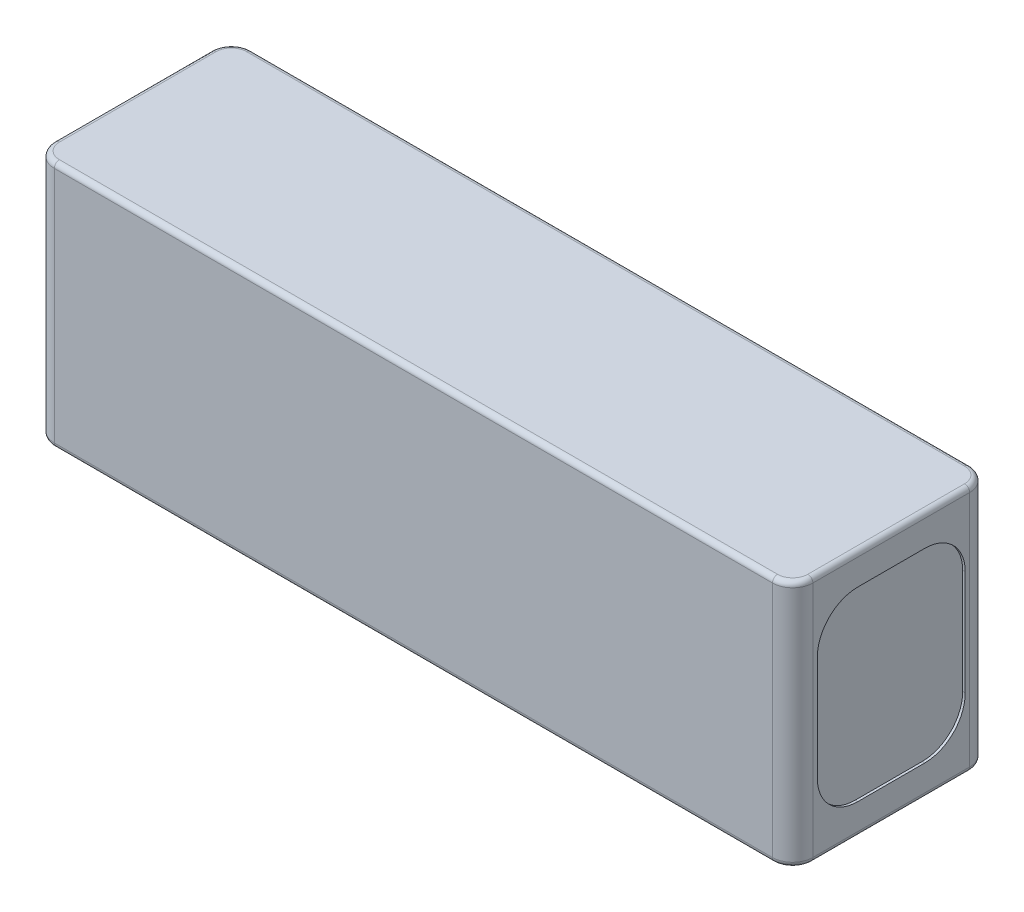
SolidWorks part; units mm, degrees
ref_plane "Front Plane" through (0, 0, 0) normal (0, 0, 1) x (1, 0, 0)
ref_plane "Top Plane" through (0, 0, 0) normal (0, 1, 0) x (1, 0, 0)
ref_plane "Right Plane" through (0, 0, 0) normal (1, 0, 0) x (0, 0, -1)
ref_plane "Plane1" through (0, 0, -15) normal (0, 0, -1) x (-1, 0, 0)
sketch "Sketch1" plane through (0, 0, -15) normal (0, 0, -1) x (-1, 0, 0)
  line L0 (-69, -22) -> (81, -22)
  line L1 (81, -22) -> (81, 27)
  line L2 (81, 27) -> (-69, 27)
  line L3 (-69, 27) -> (-69, -22)
  line L4 (-69, 2.5) -> (81, 2.5) construction
  line L5 (6, 27) -> (6, -22) construction
  dimension "D1" = 49
  dimension "D2" = 150
extrude "Boss-Extrude1" add sketch "Sketch1" against normal blind 39
sketch "Sketch2" plane through (69, 0, 0) normal (1, 0, 0) x (0, 0, -1)
  line L0 (-19.125, 12.875) -> (-19.125, -7.875)
  line L1 (-11.125, -15.875) -> (2.125, -15.875)
  line L2 (10.125, -7.875) -> (10.125, 12.875)
  line L3 (2.125, 20.875) -> (-11.125, 20.875)
  line L4 (-24, 27) -> (15, -22) construction
  line L5 (15, 27) -> (-24, -22) construction
  line L6 (-19.125, 20.875) -> (10.125, -15.875) construction
  line L7 (10.125, 20.875) -> (-19.125, -15.875) construction
  line L12 (-24, 27) -> (15, 27) construction
  line L13 (-24, 27) -> (-24, -22) construction
  line L14 (-24, -22) -> (15, -22) construction
  line L15 (15, 27) -> (15, -22) construction
  line L16 (-24, 27) -> (15, -22) construction
  line L17 (-24, -22) -> (15, 27) construction
  arc A0 (-19.125, -7.875) -> (-11.125, -15.875) centre (-11.125, -7.875) ccw
  arc A1 (2.125, -15.875) -> (10.125, -7.875) centre (2.125, -7.875) ccw
  arc A2 (10.125, 12.875) -> (2.125, 20.875) centre (2.125, 12.875) ccw
  arc A3 (-19.125, 12.875) -> (-11.125, 20.875) centre (-11.125, 12.875) cw
  point P16 (-4.5, 2.5)
  dimension "D3" = 8
  dimension "D1" = 29.25
  dimension "D2" = 39
extrude "Cut-Extrude1" cut sketch "Sketch2" against normal blind 0.5
sketch "Sketch3" plane through (-81, 0, 0) normal (-1, 0, 0) x (0, 0, 1)
  line L0 (11.125, 20.875) -> (-2.125, 20.875)
  line L1 (-10.125, 12.875) -> (-10.125, -7.875)
  line L2 (-2.125, -15.875) -> (11.125, -15.875)
  line L3 (19.125, -7.875) -> (19.125, 12.875)
  line L4 (-10.125, 20.875) -> (19.125, -15.875) construction
  line L5 (19.125, 20.875) -> (-10.125, -15.875) construction
  line L6 (-15, 27) -> (24, -22) construction
  line L7 (24, -22) -> (-15, -22) construction
  line L8 (-15, -22) -> (24, 27) construction
  arc A0 (-10.125, -7.875) -> (-2.125, -15.875) centre (-2.125, -7.875) ccw
  arc A1 (11.125, -15.875) -> (19.125, -7.875) centre (11.125, -7.875) ccw
  arc A2 (11.125, 20.875) -> (19.125, 12.875) centre (11.125, 12.875) cw
  arc A3 (-2.125, 20.875) -> (-10.125, 12.875) centre (-2.125, 12.875) ccw
  dimension "D3" = 8
  dimension "D1" = 29.25
  dimension "D2" = 39
extrude "Cut-Extrude2" cut sketch "Sketch3" against normal blind 0.5
fillet "Fillet1" radius 4 4 edges at (-81, 2.5, -15) (-81, 2.5, 24) (69, 2.5, -15) (69, 2.5, 24)
fillet "Fillet2" radius 1 16 edges at (67.8284, 27, -13.8284) (69, 27, 4.5) (-6, 27, -15) (67.8284, 27, 22.8284) (-79.8284, 27, -13.8284) (-6, 27, 24) (-81, 27, 4.5) (-79.8284, 27, 22.8284) (-81, -22, 4.5) (-79.8284, -22, -13.8284) (-79.8284, -22, 22.8284) (-6, -22, -15) (-6, -22, 24) (67.8284, -22, -13.8284) (67.8284, -22, 22.8284) (69, -22, 4.5)
equation "\"D1@Sketch3\"=\"D2@Sketch3\" * .75"
equation "\"D1@Sketch2\"=\"D2@Sketch2\"* .75"
